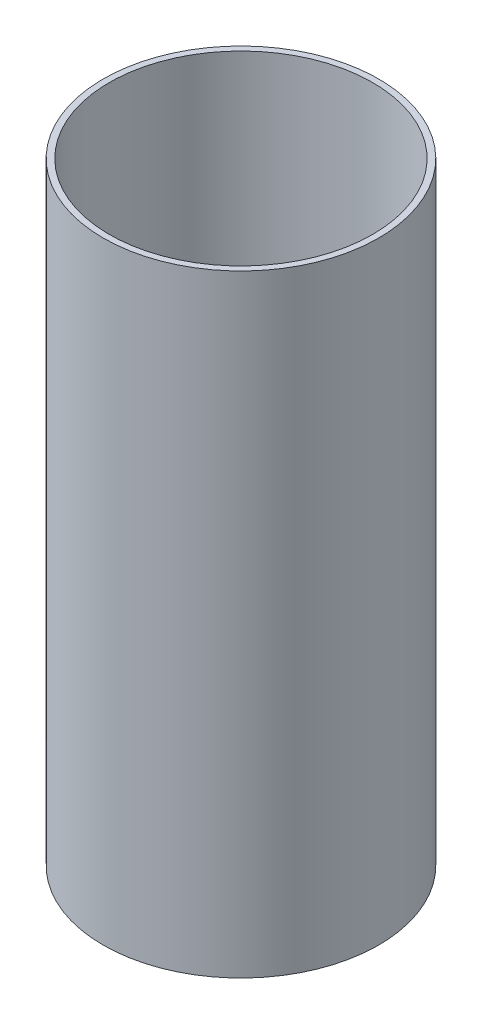
SolidWorks part; units mm, degrees
ref_plane "Ebene vorne" through (0, 0, 0) normal (0, 0, 1) x (1, 0, 0)
ref_plane "Ebene oben" through (0, 0, 0) normal (0, 1, 0) x (1, 0, 0)
ref_plane "Ebene rechts" through (0, 0, 0) normal (1, 0, 0) x (0, 0, -1)
sketch "Sketch1" plane through (0, 0, 0) normal (0, 1, 0) x (1, 0, 0)
  circle A0 centre (0, 0) radius 45
  dimension "90" = 90
extrude "Extrude-Thin1" add sketch "Sketch1" along normal blind 200 thin thin type one direction reverse wall 2
